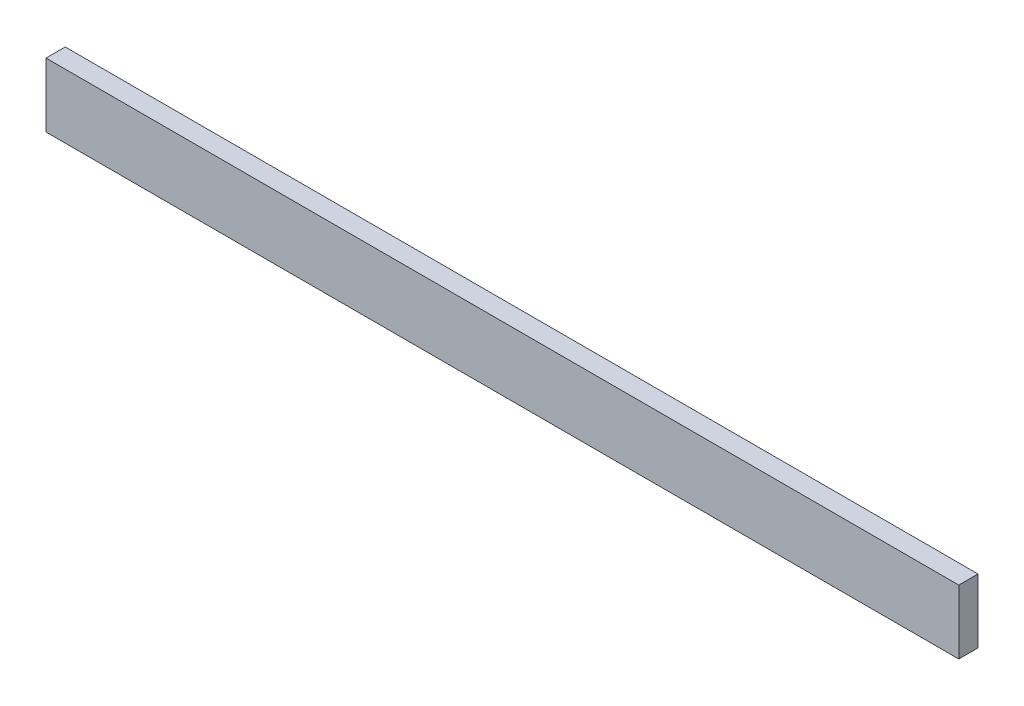
SolidWorks part; units mm, degrees
ref_plane "Front Plane" through (0, 0, 0) normal (0, 0, 1) x (1, 0, 0)
ref_plane "Top Plane" through (0, 0, 0) normal (0, 1, 0) x (1, 0, 0)
ref_plane "Right Plane" through (0, 0, 0) normal (1, 0, 0) x (0, 0, -1)
sketch "Model" plane through (0, 0, 0) normal (0, 0, 1) x (1, 0, 0)
  line L0 (28.7187, 31.6182) -> (28.7187, 11.6182)
  line L1 (28.7187, 31.6182) -> (313.7187, 31.6182)
  line L2 (313.7187, 31.6182) -> (313.7187, 11.6182)
  line L3 (313.7187, 11.6182) -> (28.7187, 11.6182)
extrude "Boss-Extrude1" add sketch "Model" along normal blind 6 contours L0 L3 L2 L1
